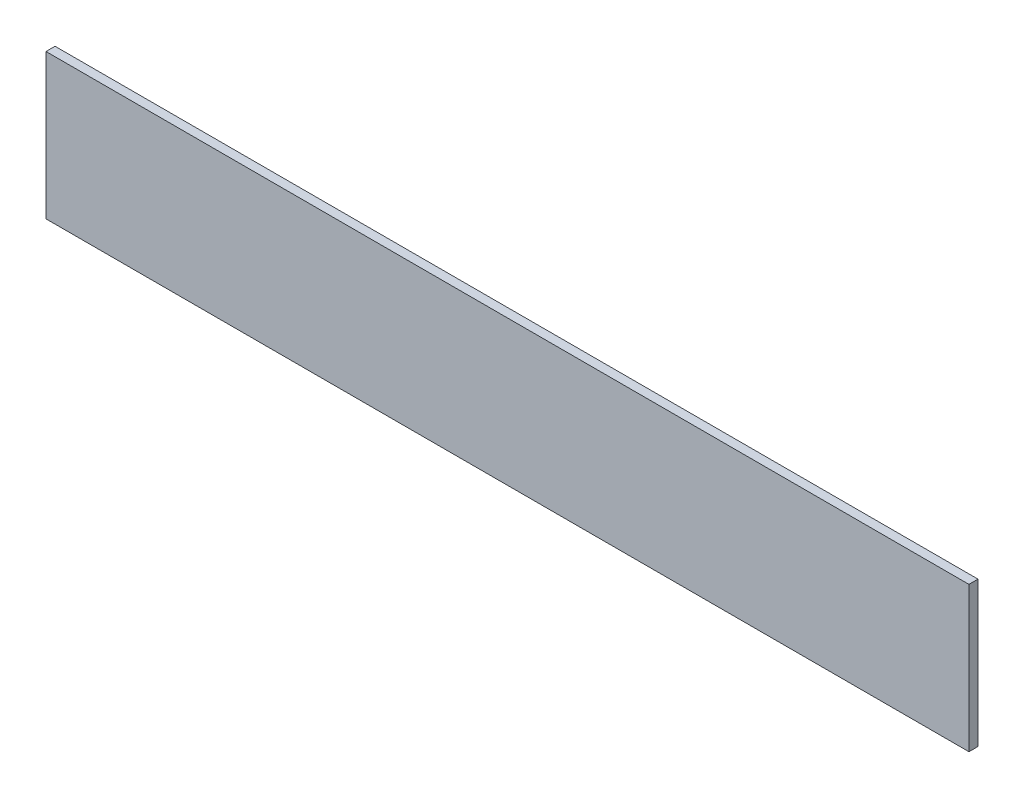
SolidWorks part; units mm, degrees
ref_plane "Front Plane" through (0, 0, 0) normal (0, 0, 1) x (1, 0, 0)
ref_plane "Top Plane" through (0, 0, 0) normal (0, 1, 0) x (1, 0, 0)
ref_plane "Right Plane" through (0, 0, 0) normal (1, 0, 0) x (0, 0, -1)
sketch "Sketch1" plane through (0, 0, 0) normal (0, 0, 1) x (1, 0, 0)
  line L0 (0, 0) -> (0, 101.6) construction
  line L1 (0, 0) -> (646.8661, 0)
  line L2 (0, 0) -> (0, 101.6)
  line L3 (0, 101.6) -> (646.8661, 101.6)
  line L4 (646.8661, 0) -> (646.8661, 101.6)
  line L5 (646.8661, 10.6454) -> (646.8661, 112.2454) construction
  dimension "D1" = 101.6
extrude "Boss-Extrude1" add sketch "Sketch1" along normal blind 6.35
